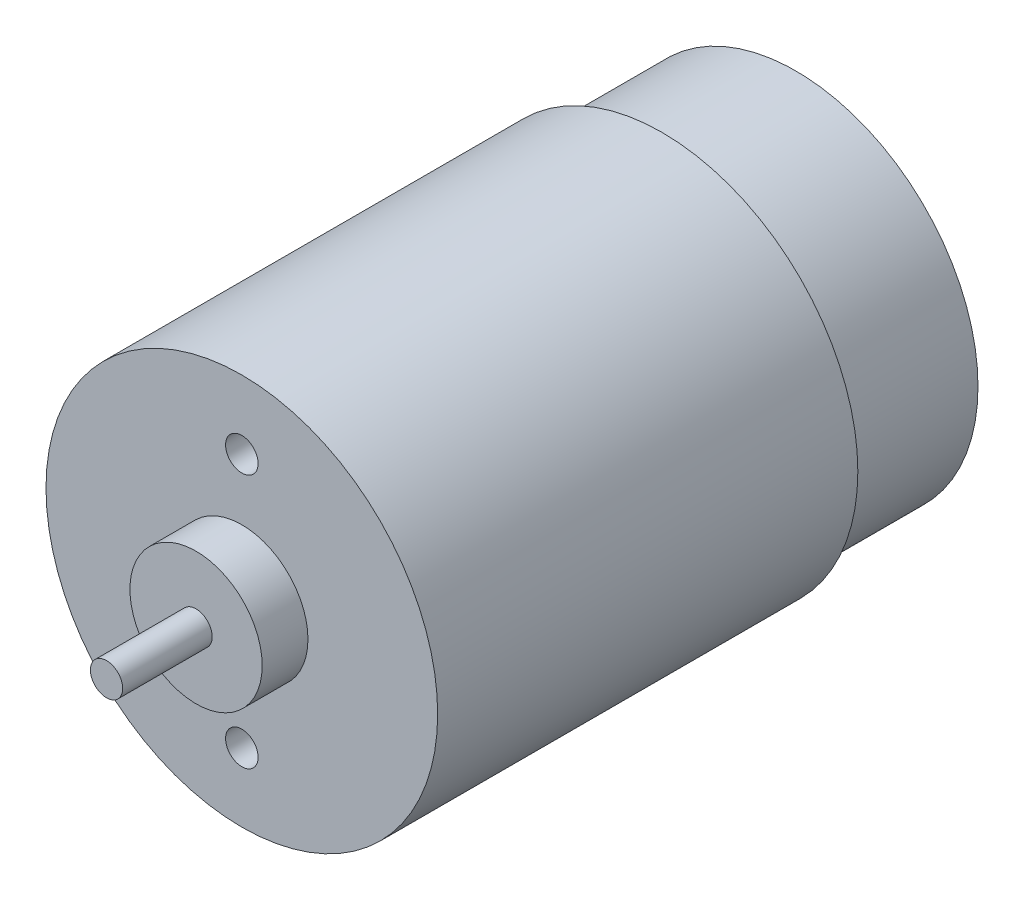
SolidWorks part; units mm, degrees
ref_plane "Front Plane" through (0, 0, 0) normal (0, 0, 1) x (1, 0, 0)
ref_plane "Top Plane" through (0, 0, 0) normal (0, 1, 0) x (1, 0, 0)
ref_plane "Right Plane" through (0, 0, 0) normal (1, 0, 0) x (0, 0, -1)
sketch "Sketch1" plane through (0, 0, 0) normal (0, 0, 1) x (1, 0, 0)
  circle A0 centre (0, 0) radius 19.25
  dimension "D1" = 38.5
extrude "Boss-Extrude1" add sketch "Sketch1" along normal blind 41.3 contours A0
sketch "Sketch3" plane through (0, 0, 41.3) normal (0, 0, 1) x (1, 0, 0)
  circle A0 centre (0, 0) radius 1.585
  dimension "D1" = 3.17
extrude "Boss-Extrude2" add sketch "Sketch3" along normal blind 13.3 contours A0
sketch "Sketch4" plane through (0, 0, 41.3) normal (0, 0, 1) x (1, 0, 0)
  circle A0 centre (0, 0) radius 6.5
  dimension "D1" = 13
extrude "Boss-Extrude3" add sketch "Sketch4" along normal blind 4.5 contours A0
sketch "Sketch5" plane through (0, 0, 0) normal (0, 0, -1) x (-1, 0, 0)
  circle A0 centre (0, 0) radius 17.9
  dimension "D1" = 35.8
extrude "Boss-Extrude4" add sketch "Sketch5" along normal blind 13.16
sketch "Sketch6" plane through (0, 0, -13.16) normal (0, 0, -1) x (-1, 0, 0)
  circle A0 centre (0, 0) radius 5.1
  dimension "D1" = 10.2
extrude "Boss-Extrude5" add sketch "Sketch6" along normal blind 3
sketch "Sketch7" plane through (0, 0, -16.16) normal (0, 0, -1) x (-1, 0, 0)
  circle A0 centre (0, 0) radius 2.375
  dimension "D1" = 4.75
extrude "Boss-Extrude6" add sketch "Sketch7" along normal blind 3
sketch "Sketch8" plane through (0, 0, 41.3) normal (0, 0, 1) x (1, 0, 0)
  circle A0 centre (0, 12.5) radius 1.6
  circle A2 centre (0, -12.5) radius 1.6
  point P8 (0, 0)
  dimension "D2" = 3.2
  dimension "D1" = 12.5
  dimension "D4" = 2
extrude "Cut-Extrude1" cut sketch "Sketch8" against normal blind 3
